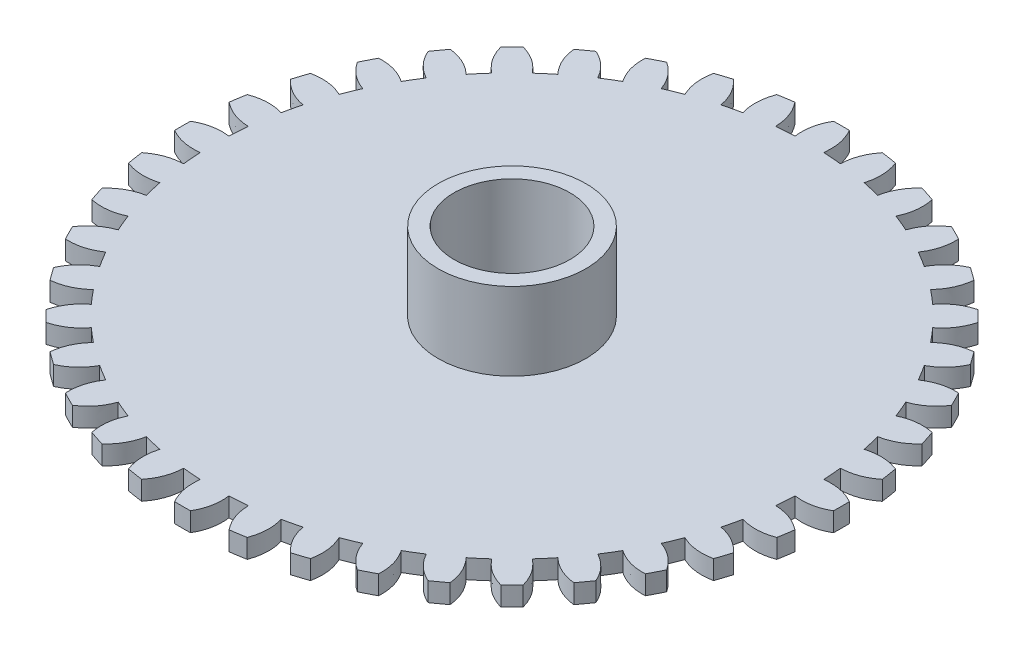
SolidWorks part; units mm, degrees
ref_plane "Front Plane" through (0, 0, 0) normal (0, 0, 1) x (1, 0, 0)
ref_plane "Top Plane" through (0, 0, 0) normal (0, 1, 0) x (1, 0, 0)
ref_plane "Right Plane" through (0, 0, 0) normal (1, 0, 0) x (0, 0, -1)
sketch "Sketch2" plane through (0, 0, 0) normal (0, 1, 0) x (1, 0, 0)
  circle A0 centre (0, 0) radius 3.75
  dimension "D1" = 7.5
extrude "Boss-Extrude1" add sketch "Sketch2" along normal blind 0.24
sketch "Sketch1" plane through (0, 0, 0) normal (0, 1, 0) x (1, 0, 0)
  line L0 (0, 0) -> (0, -4.15) construction
  circle A0 centre (0, 0) radius 4.15 construction
  circle A1 centre (0, 0) radius 3.75 construction
  arc A2 (-0.1, -4.1488) -> (0.1, -4.1488) centre (0, 0) ccw
  arc A3 (-0.18, -3.7457) -> (0.18, -3.7457) centre (0, 0) ccw
  spline S0 degree 2 poles (-0.18, -3.7457) (-0.2076, -3.9601) (-0.1, -4.1488) knots 0 0 0 1 1 1
  spline S1 degree 2 poles (0.18, -3.7457) (0.2076, -3.9601) (0.1, -4.1488) knots 0 0 0 1 1 1
  dimension "D1" = 8.3
  dimension "D2" = 7.5
  dimension "D3" = 0.18
  dimension "D4" = 0.1
extrude "Boss-Extrude2" add sketch "Sketch1" along normal blind 0.24
pattern_circular "CirPattern1" count 40 over 360 about axis through (0, 0.24, 0) along (0, -1, 0) of "Boss-Extrude2"
sketch "Sketch3" plane through (0, 0.24, 0) normal (0, 1, 0) x (1, 0, 0)
  circle A0 centre (0, 0) radius 0.93
  dimension "D1" = 1.86
extrude "Boss-Extrude3" add sketch "Sketch3" along normal blind 0.98
sketch "Sketch4" plane through (0, 1.22, 0) normal (0, 1, 0) x (1, 0, 0)
  circle A0 centre (0, 0) radius 0.73
  dimension "D1" = 1.46
extrude "Cut-Extrude1" cut sketch "Sketch4" against normal through all
